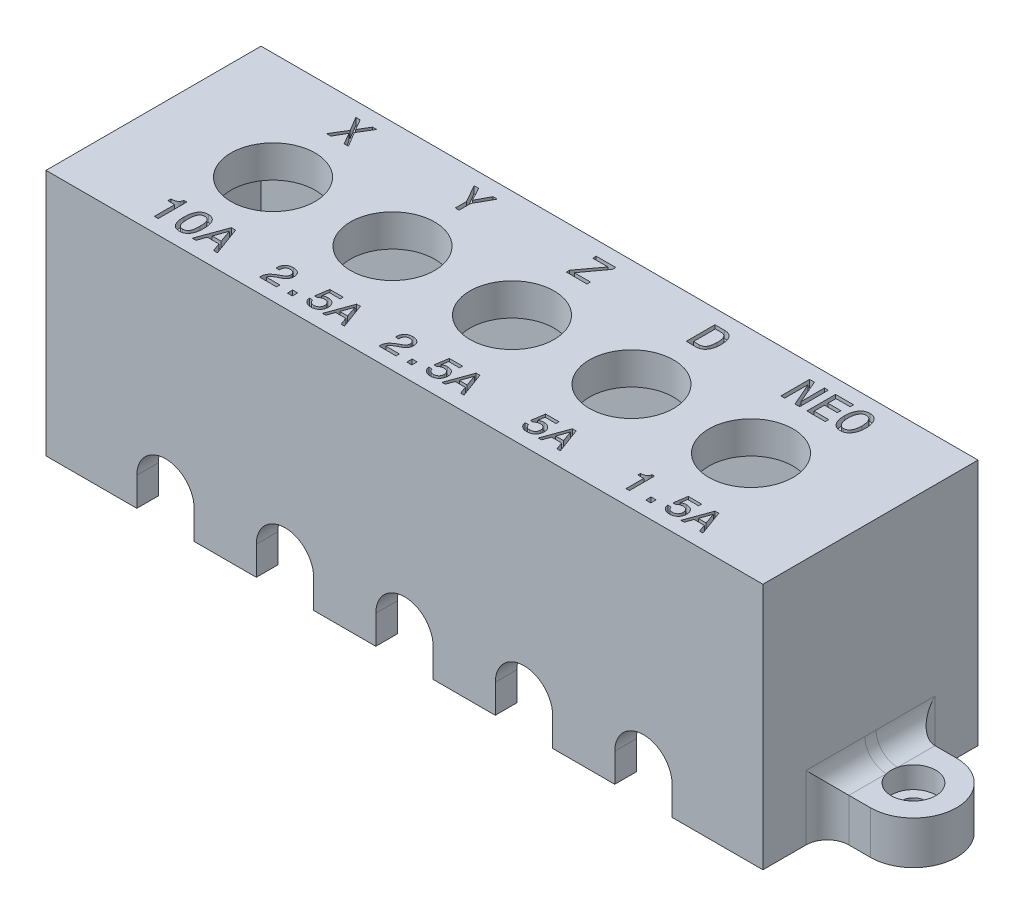
SolidWorks part; units mm, degrees
ref_plane "Front Plane" through (0, 0, 0) normal (0, 0, 1) x (1, 0, 0)
ref_plane "Top Plane" through (0, 0, 0) normal (0, 1, 0) x (1, 0, 0)
ref_plane "Right Plane" through (0, 0, 0) normal (1, 0, 0) x (0, 0, -1)
sketch "Sketch1" plane through (0, 0, 0) normal (0, 1, 0) x (1, 0, 0)
  line L1 (-100, 15) -> (0, 15)
  line L2 (-100, 15) -> (-100, -15)
  line L3 (-100, -15) -> (0, -15)
  line L4 (0, 15) -> (0, -15)
  point P4 (0, 0)
  dimension "D1" = 100
  dimension "D2" = 30
extrude "Boss-Extrude1" add sketch "Sketch1" along normal blind 4.5
sketch "Sketch2" plane through (0, 4.5, 0) normal (0, 1, 0) x (1, 0, 0)
  line L0 (-100, 0) -> (0, 0) construction
  line L1 (-100, 15) -> (-100, -15) construction
  circle A0 centre (-83.3333, 0) radius 5.875
  circle A1 centre (-66.6667, 0) radius 5.875
  circle A2 centre (-50, 0) radius 5.875
  circle A3 centre (-33.3333, 0) radius 5.875
  circle A4 centre (-16.6667, 0) radius 5.875
  dimension "D7" = 11.75
  dimension "D1" = 100
  dimension "D2" = 16.6667
  dimension "D3" = 33.3333
  dimension "D4" = 50
  dimension "D5" = 66.6667
  dimension "D6" = 83.3333
extrude "Cut-Extrude1" cut sketch "Sketch2" against normal through all
sketch "Sketch3" plane through (0, 4.5, 0) normal (0, 1, 0) x (1, 0, 0)
  line L0 (-89.2083, 0) -> (-89.2083, 15) construction
  line L1 (0, 15) -> (-100, 15) construction
  line L2 (-77.4583, 0) -> (-77.4583, 15) construction
  line L3 (-77.4583, 9) -> (-89.2083, 9) construction
  line L4 (-72.5417, 0) -> (-72.5417, 15) construction
  line L5 (-60.7917, 0) -> (-60.7917, 15) construction
  line L6 (-72.5417, 9) -> (-60.7917, 9) construction
  line L7 (-55.875, 0) -> (-55.875, 15) construction
  line L8 (-44.125, 0) -> (-44.125, 15) construction
  line L9 (-55.875, 9) -> (-44.125, 9) construction
  line L10 (-39.2083, 0) -> (-39.2083, 15) construction
  line L11 (-27.4583, 0) -> (-27.4583, 15) construction
  line L12 (-39.2083, 9) -> (-27.4583, 9) construction
  line L13 (-22.5417, 0) -> (-22.5417, 15) construction
  line L14 (-10.7917, 0) -> (-10.7917, 15) construction
  line L15 (-22.5417, 9) -> (-10.7917, 9) construction
  line L16 (-89.2083, 0) -> (-89.2083, -15) construction
  line L17 (-100, -15) -> (0, -15) construction
  line L18 (-77.4583, 0) -> (-77.4583, -15) construction
  line L19 (-72.5417, 0) -> (-72.5417, -15) construction
  line L20 (-60.7917, 0) -> (-60.7917, -15) construction
  line L21 (-55.875, 0) -> (-55.875, -15) construction
  line L22 (-44.125, 0) -> (-44.125, -15) construction
  line L23 (-39.2083, 0) -> (-39.2083, -15) construction
  line L24 (-27.4583, 0) -> (-27.4583, -15) construction
  line L25 (-22.5417, 0) -> (-22.5417, -15) construction
  line L26 (-10.7917, 0) -> (-10.7917, -15) construction
  line L27 (-89.2083, -13) -> (-77.4583, -13) construction
  line L28 (-72.5417, -13) -> (-60.7917, -13) construction
  line L29 (-55.875, -13) -> (-44.125, -13) construction
  line L30 (-39.2083, -13) -> (-27.4583, -13) construction
  line L31 (-22.5417, -13) -> (-10.7917, -13) construction
  circle A0 centre (-83.3333, 0) radius 5.875 construction
  circle A1 centre (-66.6667, 0) radius 5.875 construction
  circle A2 centre (-50, 0) radius 5.875 construction
  circle A3 centre (-33.3333, 0) radius 5.875 construction
  circle A4 centre (-16.6667, 0) radius 5.875 construction
  text T0 "X" font "Monospac821 BT" height 4
  text T1 "Y" font "Monospac821 BT" height 4
  text T2 "Z" font "Monospac821 BT" height 4
  text T3 "D" font "Monospac821 BT" height 4
  text T4 "NEO" font "Monospac821 BT" height 4
  text T5 "10A" font "Monospac821 BT" height 4
  text T6 "2.5A" font "Monospac821 BT" height 3.5
  text T7 "2.5A" font "Monospac821 BT" height 3.5
  text T8 "5A" font "Monospac821 BT" height 3.5
  text T9 "1.5A" font "Monospac821 BT" height 3.5
  dimension "D1" = 2
  dimension "D2" = 6
extrude "Cut-Extrude2" cut sketch "Sketch3" against normal blind 1
sketch "Sketch4" plane through (0, 0, 0) normal (0, -1, 0) x (1, 0, 0)
  line L0 (-100, 15) -> (-100, -15)
  line L1 (-100, -15) -> (0, -15)
  line L2 (0, -15) -> (0, 15)
  line L3 (-97, 12) -> (-97, -12)
  line L4 (-97, -12) -> (-3, -12)
  line L5 (-3, -12) -> (-3, 12)
  line L9 (-97, 15) -> (-97, -12) construction
  line L10 (-100, 12) -> (0, 12)
  line L11 (-97, 12) -> (-3, 12)
  line L12 (-3, -12) -> (-3, 15) construction
  line L15 (-100, 15) -> (0, 15)
  dimension "D1" = 3
  dimension "D2" = 3
extrude "Boss-Extrude2" add sketch "Sketch4" along normal blind 30
sketch "Sketch5" plane through (0, -30, 0) normal (0, -1, 0) x (1, 0, 0)
  line L0 (-100, -15) -> (0, -15) construction
  line L1 (-56, -21) -> (-56, -15)
  line L2 (-44, -21) -> (-44, -15)
  line L3 (-44, -15) -> (-56, -15)
  line L4 (-106, 6) -> (-100, 6)
  line L5 (-100, 15) -> (-100, -15) construction
  line L6 (-100, 6) -> (-100, -6)
  line L7 (-100, -6) -> (-106, -6)
  line L8 (6, 6) -> (0, 6)
  line L9 (0, -15) -> (0, 15) construction
  line L10 (0, 6) -> (0, -6)
  line L11 (0, -6) -> (6, -6)
  arc A0 (-56, -21) -> (-44, -21) centre (-50, -21) ccw
  arc A1 (6, -6) -> (6, 6) centre (6, 0) ccw
  arc A2 (-106, 6) -> (-106, -6) centre (-106, 0) ccw
  point P4 (-50, -15)
  point P10 (-100, 0)
  point P11 (0, 0)
  point P22 (0, 0)
  dimension "D1" = 6
  dimension "D2" = 6
extrude "Boss-Extrude3" add sketch "Sketch5" against normal blind 6
sketch "Sketch6" plane through (0, -24, 0) normal (0, 1, 0) x (1, 0, 0)
  point P0 (6, 0)
  point P3 (-50, 21)
  point P6 (-106, 0)
hole_wizard "CBORE for M3 SHCS1" positions "Sketch6" profile "Sketch7" counterbore size "M3" standard "ANSI Metric" end condition through all
sketch "Sketch7" plane through (6, -24, 0) normal (1, 0, 0) x (0, 0, 1)
  line L0 (0, 0) -> (0, 6)
  line L1 (0, 6) -> (1.7, 6)
  line L3 (1.7, 6) -> (1.7, 3)
  line L4 (1.7, 3) -> (3.1, 3)
  line L5 (3.1, 3) -> (3.1, 0)
  line L7 (3.1, 0) -> (0, 0)
  line L11 (0, -6.35) -> (0, 107.95) construction
  dimension "Thru Hole Dia." = 3.4
  dimension "Thru Hole Depth" = 6
  dimension "C'Bore Dia." = 6.2
  dimension "C'Bore Depth" = 3
fillet "Fillet2" radius 3 9 edges at (-100, -27, 6) (-100, -24, 0) (-100, -27, -6) (-56, -27, -15) (-50, -24, -15) (-44, -27, -15) (0, -27, -6) (0, -24, 0) (0, -27, 6)
sketch "Sketch8" plane through (0, 0, 15) normal (0, 0, 1) x (1, 0, 0)
  line L0 (-87.3333, -26) -> (-87.3333, -30)
  line L1 (0, -30) -> (-100, -30) construction
  line L2 (-79.3333, -26) -> (-79.3333, -30)
  line L3 (-79.3333, -30) -> (-87.3333, -30)
  line L5 (-100, 4.5) -> (-100, -30) construction
  arc A0 (-79.3333, -26) -> (-87.3333, -26) centre (-83.3333, -26) ccw
  dimension "D1" = 4
  dimension "D2" = 4
  dimension "D3" = 16.6667
extrude "Cut-Extrude3" cut sketch "Sketch8" against normal up to surface (3 mm away) up to face at (-50, -15, 12)
pattern_linear "LPattern1" count 5 spacing 16.6667 along (1, 0, 0) of "Cut-Extrude3"
sketch "Sketch10" plane through (0, -30, 0) normal (0, -1, 0) x (1, 0, 0)
  line L0 (-41, -15) -> (0, -15) construction
  line L1 (-40, -15) -> (-60, -15)
  line L2 (-40, -15) -> (-40, -30)
  line L3 (-40, -30) -> (-60, -30)
  line L4 (-60, -15) -> (-60, -30)
  line L5 (-50, -27) -> (-50, -13.8996) construction
  arc A0 (-56, -21) -> (-44, -21) centre (-50, -21) ccw construction
  point P12 (-50, -30)
  dimension "D1" = 20
  dimension "D2" = 15
extrude "Cut-Extrude4" cut sketch "Sketch10" against normal up to next
equation "\"D2@Sketch2\"=\"D1@Sketch2\"/6"
equation "\"D3@Sketch2\"=\"D1@Sketch2\"/6*2"
equation "\"D4@Sketch2\"=\"D1@Sketch2\"/6*3"
equation "\"D5@Sketch2\"=\"D1@Sketch2\"/6*4"
equation "\"D6@Sketch2\"=\"D1@Sketch2\"/6*5"
equation "\"D2@Sketch5\"=\"D1@Sketch5\""
equation "\"D2@Sketch8\"=\"D1@Sketch8\""
equation "\"D3@Sketch8\"=100/6"
equation "\"D3@LPattern1\"=16+2/3"
